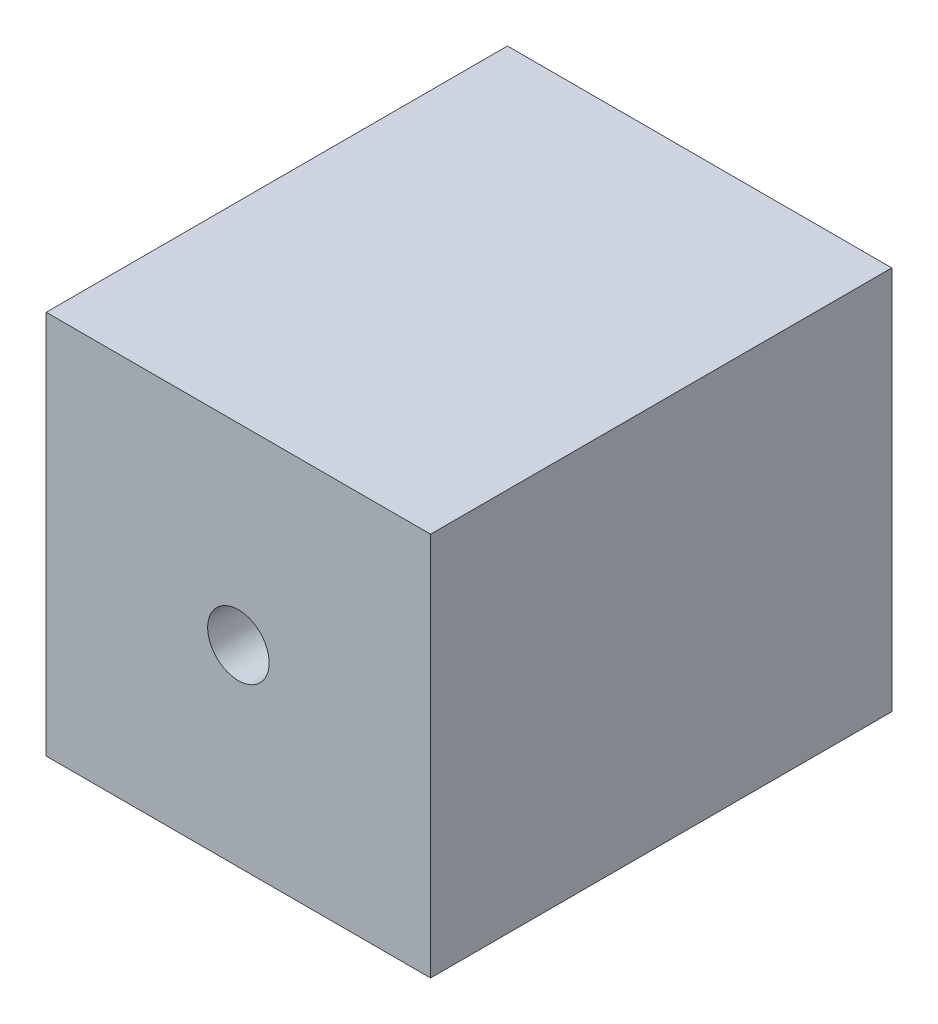
SolidWorks part; units mm, degrees
ref_plane "Front Plane" through (0, 0, 0) normal (0, 0, 1) x (1, 0, 0)
ref_plane "Top Plane" through (0, 0, 0) normal (0, 1, 0) x (1, 0, 0)
ref_plane "Right Plane" through (0, 0, 0) normal (1, 0, 0) x (0, 0, -1)
sketch "Sketch1" plane through (0, 0, 0) normal (0, 0, 1) x (1, 0, 0)
  line L1 (5, 5) -> (-5, 5)
  line L2 (5, 5) -> (5, -5)
  line L3 (5, -5) -> (-5, -5)
  line L4 (-5, 5) -> (-5, -5)
  line L5 (5, 5) -> (-5, -5) construction
  line L6 (5, -5) -> (-5, 5) construction
  point P0 (0, 0)
  dimension "D1" = 10
  dimension "D2" = 10
extrude "Boss-Extrude1" add sketch "Sketch1" along normal blind 12
hole_wizard "#10-32 Tapped Hole1" positions "Sketch2" profile "Sketch3" tap size "#10-32" standard "ANSI Inch"
sketch "Sketch2" plane through (0, 0, 0) normal (0, 0, 1) x (1, 0, 0)
  point P0 (0, 0)
sketch "Sketch3" plane through (0, 0, 0) normal (1, 0, 0) x (0, 1, 0)
  line L0 (0, 0) -> (0, 6.2133)
  line L1 (0, 6.2133) -> (2.0193, 5)
  line L2 (2.0193, 5) -> (2.0193, 0)
  line L5 (2.0193, 0) -> (0, 0)
  line L10 (0, 6.2133) -> (-2.0193, 5) construction
  line L11 (0, -6.35) -> (0, 107.95) construction
  dimension "Tap Drill Dia." = 4.0386
  dimension "Tap Drill Depth" = 5
  dimension "Drill Angle" = 118
cosmetic thread "Hole Thread1" parameters "D1"=4, "D2"=4.826
hole_wizard "M2x0.4 Tapped Hole1" positions "Sketch4" profile "Sketch5" tap size "M2x0.4" standard "ANSI Metric"
sketch "Sketch4" plane through (0, 0, 12) normal (0, 0, 1) x (1, 0, 0)
  point P0 (0, 0)
sketch "Sketch5" plane through (0, 0, 12) normal (1, 0, 0) x (0, -1, 0)
  line L0 (0, 0) -> (0, 7.4807)
  line L1 (0, 7.4807) -> (0.8, 7)
  line L2 (0.8, 7) -> (0.8, 0)
  line L5 (0.8, 0) -> (0, 0)
  line L10 (0, 7.4807) -> (-0.8, 7) construction
  line L11 (0, -6.35) -> (0, 107.95) construction
  dimension "Tap Drill Dia." = 1.6
  dimension "Tap Drill Depth" = 7
  dimension "Drill Angle" = 118
cosmetic thread "Hole Thread2" parameters "D1"=4, "D2"=2
